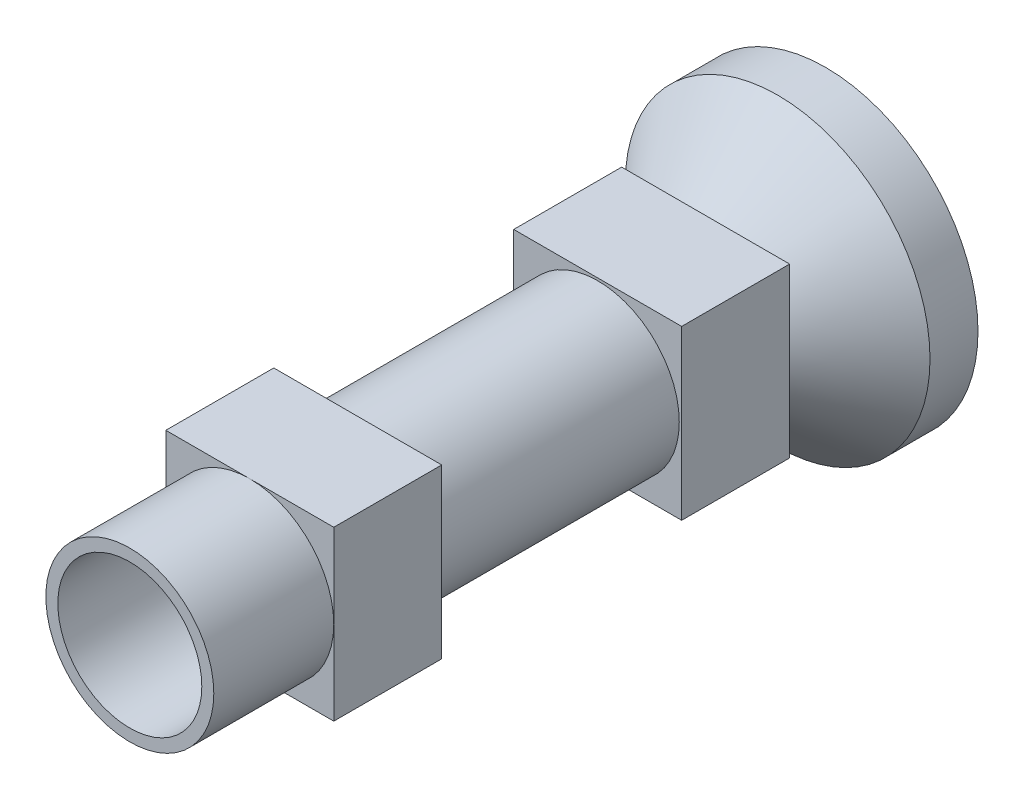
SolidWorks part; units mm, degrees
material "ABS"
ref_plane "正面" through (0, 0, 0) normal (0, 0, 1) x (1, 0, 0)
ref_plane "平面" through (0, 0, 0) normal (0, 1, 0) x (1, 0, 0)
ref_plane "右側面" through (0, 0, 0) normal (1, 0, 0) x (0, 0, -1)
sketch "ｽｹｯﾁ1" plane through (0, 0, 0) normal (0, 0, 1) x (1, 0, 0)
  circle A0 centre (0, 0) radius 3.5 construction
  circle A1 centre (0, 0) radius 6.35
  dimension "D1" = 7
  dimension "D2" = 12.7
ref_plane "平面1" through (0, 0, 5) normal (0, 0, 1) x (1, 0, 0)
sketch "ｽｹｯﾁ2" plane through (0, 0, 5) normal (0, 0, 1) x (1, 0, 0)
  circle A0 centre (0, 0) radius 3.5 construction
  circle A1 centre (0, 0) radius 3.5
ref_plane "平面2" through (0, 0, 29) normal (0, 0, 1) x (1, 0, 0)
ref_plane "平面3" through (0, 0, 24) normal (0, 0, 1) x (1, 0, 0)
sketch "ｽｹｯﾁ5" plane through (0, 0, 29) normal (0, 0, 1) x (1, 0, 0)
  circle A0 centre (0, 0) radius 6.35 construction
  circle A1 centre (0, 0) radius 6.35 construction
  circle A2 centre (0, 0) radius 3.5
  dimension "D1" = 7
extrude "ﾎﾞｽ - 押し出し3" add sketch "ｽｹｯﾁ2" along normal up to surface (19 mm away) contours A1 up to plane "平面3"
extrude "ﾎﾞｽ - 押し出し4" add sketch "ｽｹｯﾁ1" along normal blind 2 separate body
extrude "ﾎﾞｽ - 押し出し5" add sketch "ｽｹｯﾁ5" against normal blind 2 contours A1
loft "ﾛﾌﾄ1" add section face at (6.35, 0, 2) section face at (3.5, 0, 5)
loft "ﾛﾌﾄ2" add section face at (3.5, 0, 24) section face at (3.5, 0, 27)
ref_plane "平面5" through (0, 0, 14.5) normal (0, 0, 1) x (1, 0, 0)
ref_plane "平面6" through (0, 0, 15.25) normal (0, 0, 1) x (1, 0, 0)
sketch "ｽｹｯﾁ6" plane through (0, 0, 0) normal (0, 0, -1) x (-1, 0, 0)
  circle A0 centre (0, 0) radius 2.75
  dimension "D1" = 5.5
extrude "ｶｯﾄ - 押し出し1" cut sketch "ｽｹｯﾁ6" against normal blind 3
sketch "ｽｹｯﾁ7" plane through (0, 0, 3) normal (0, 0, -1) x (-1, 0, 0)
  circle A0 centre (0, 0) radius 1.8
  dimension "D1" = 3.6
extrude "ｶｯﾄ - 押し出し2" cut sketch "ｽｹｯﾁ7" against normal through all
sketch "ｽｹｯﾁ8" plane through (0, 0, 29) normal (0, 0, 1) x (1, 0, 0)
  circle A0 centre (0, 0) radius 3
  dimension "D1" = 6
extrude "ｶｯﾄ - 押し出し3" cut sketch "ｽｹｯﾁ8" against normal offset from surface (23 mm away) 3 up to face at (-1.8, 0, 3)
sketch "ｽｹｯﾁ12" plane through (0, 0, 0) normal (0, 0, -1) x (-1, 0, 0)
  line L0 (0, 0) -> (0, 2.75) construction
  line L1 (0, 0) -> (0.3745, 2.7244) construction
  line L2 (0, 0) -> (0.7419, 2.648) construction
  line L3 (0, 0) -> (1.0956, 2.5223) construction
  line L4 (0, 0) -> (1.4289, 2.3497) construction
  line L5 (0, 0) -> (1.7355, 2.1332) construction
  line L6 (0, 0) -> (2.0098, 1.877) construction
  line L7 (0, 0) -> (2.2467, 1.5859) construction
  line L8 (0, 0) -> (2.4417, 1.2652) construction
  line L9 (0, 0) -> (2.5912, 0.9209) construction
  line L10 (0, 0) -> (2.6925, 0.5595) construction
  line L11 (0, 0) -> (2.7436, 0.1877) construction
  line L12 (0, 0) -> (2.7436, -0.1877) construction
  line L13 (0, 0) -> (2.6925, -0.5595) construction
  line L14 (0, 0) -> (2.5912, -0.9209) construction
  line L15 (0, 0) -> (2.4417, -1.2652) construction
  line L16 (0, 0) -> (2.2467, -1.5859) construction
  line L17 (0, 0) -> (2.0098, -1.877) construction
  line L18 (0, 0) -> (1.7355, -2.1332) construction
  line L19 (0, 0) -> (1.4289, -2.3497) construction
  line L20 (0, 0) -> (1.0956, -2.5223) construction
  line L21 (0, 0) -> (0.7419, -2.648) construction
  line L22 (0, 0) -> (0.3745, -2.7244) construction
  line L23 (0, 0) -> (0, -2.75) construction
  line L24 (0, 0) -> (-0.3745, -2.7244) construction
  line L25 (0, 0) -> (-0.7419, -2.648) construction
  line L26 (0, 0) -> (-1.0956, -2.5223) construction
  line L27 (0, 0) -> (-1.4289, -2.3497) construction
  line L28 (0, 0) -> (-1.7355, -2.1332) construction
  line L29 (0, 0) -> (-2.0098, -1.877) construction
  line L30 (0, 0) -> (-2.2467, -1.5859) construction
  line L31 (0, 0) -> (-2.4417, -1.2652) construction
  line L32 (0, 0) -> (-2.5912, -0.9209) construction
  line L33 (0, 0) -> (-2.6925, -0.5595) construction
  line L34 (0, 0) -> (-2.7436, -0.1877) construction
  line L35 (0, 0) -> (-2.7436, 0.1877) construction
  line L36 (0, 0) -> (-2.6925, 0.5595) construction
  line L37 (0, 0) -> (-2.5912, 0.9209) construction
  line L38 (0, 0) -> (-2.4417, 1.2652) construction
  line L39 (0, 0) -> (-2.2467, 1.5859) construction
  line L40 (0, 0) -> (-2.0098, 1.877) construction
  line L41 (0, 0) -> (-1.7355, 2.1332) construction
  line L42 (0, 0) -> (-1.4289, 2.3497) construction
  line L43 (0, 0) -> (-1.0956, 2.5223) construction
  line L44 (0, 0) -> (-0.7419, 2.648) construction
  line L45 (0, 0) -> (-0.3745, 2.7244) construction
  line L46 (0, 0) -> (0.2081, 3.0429) construction
  line L47 (0.2081, 3.0429) -> (-0.0626, 2.7493)
  line L48 (-0.0626, 2.7493) -> (0, 0) construction
  line L49 (0, 0) -> (0.4364, 2.7152) construction
  line L50 (0.4364, 2.7152) -> (0.2081, 3.0429)
  line L51 (1.0214, 2.8739) -> (0.6815, 2.6642)
  line L52 (1.1527, 2.4967) -> (1.0214, 2.8739)
  line L53 (1.7589, 2.4918) -> (1.375, 2.3816)
  line L54 (1.7836, 2.0931) -> (1.7589, 2.4918)
  line L55 (2.3659, 1.9248) -> (1.9666, 1.9223)
  line L56 (2.2822, 1.5343) -> (2.3659, 1.9248)
  line L57 (2.7975, 1.2151) -> (2.4123, 1.3204)
  line L58 (2.6115, 0.8617) -> (2.7975, 1.2151)
  line L59 (3.0216, 0.4153) -> (2.679, 0.6206)
  line L60 (2.7472, 0.1252) -> (3.0216, 0.4153)
  line L61 (3.0216, -0.4153) -> (2.7472, -0.1252)
  line L62 (2.679, -0.6206) -> (3.0216, -0.4153)
  line L63 (2.7975, -1.2151) -> (2.6115, -0.8617)
  line L64 (2.4123, -1.3204) -> (2.7975, -1.2151)
  line L65 (2.3659, -1.9248) -> (2.2822, -1.5343)
  line L66 (1.9666, -1.9223) -> (2.3659, -1.9248)
  line L67 (1.7589, -2.4918) -> (1.7836, -2.0931)
  line L68 (1.375, -2.3816) -> (1.7589, -2.4918)
  line L69 (1.0214, -2.8739) -> (1.1527, -2.4967)
  line L70 (0.6815, -2.6642) -> (1.0214, -2.8739)
  line L71 (0.2081, -3.0429) -> (0.4364, -2.7152)
  line L72 (-0.0626, -2.7493) -> (0.2081, -3.0429)
  line L73 (-0.6205, -2.9862) -> (-0.3123, -2.7322)
  line L74 (-0.802, -2.6304) -> (-0.6205, -2.9862)
  line L75 (-1.4032, -2.708) -> (-1.0379, -2.5466)
  line L76 (-1.482, -2.3165) -> (-1.4032, -2.708)
  line L77 (-2.0818, -2.229) -> (-1.6865, -2.1722)
  line L78 (-2.052, -1.8308) -> (-2.0818, -2.229)
  line L79 (-2.606, -1.5847) -> (-2.21, -1.6366)
  line L80 (-2.4699, -1.2093) -> (-2.606, -1.5847)
  line L81 (-2.9369, -0.8229) -> (-2.5696, -0.9797)
  line L82 (-2.7045, -0.4981) -> (-2.9369, -0.8229)
  line L83 (-3.05, 0) -> (-2.7386, -0.2501)
  line L84 (-2.7386, 0.2501) -> (-3.05, 0)
  line L85 (-2.9369, 0.8229) -> (-2.7045, 0.4981)
  line L86 (-2.5696, 0.9797) -> (-2.9369, 0.8229)
  line L87 (-2.606, 1.5847) -> (-2.4699, 1.2093)
  line L88 (-2.21, 1.6366) -> (-2.606, 1.5847)
  line L89 (-2.0818, 2.229) -> (-2.052, 1.8308)
  line L90 (-1.6865, 2.1722) -> (-2.0818, 2.229)
  line L91 (-1.4032, 2.708) -> (-1.482, 2.3165)
  line L92 (-1.0379, 2.5466) -> (-1.4032, 2.708)
  line L93 (-0.6205, 2.9862) -> (-0.802, 2.6304)
  line L94 (-0.3123, 2.7322) -> (-0.6205, 2.9862)
  circle A0 centre (0, 0) radius 2.75 construction
  circle A1 centre (0, 0) radius 3.05 construction
  arc A2 (0, 2.75) -> (0.3745, 2.7244) centre (0, 0) cw construction
  circle A3 centre (0, 0) radius 2.75 construction
  arc A4 (-0.0626, 2.7493) -> (0.4364, 2.7152) centre (0, 0) cw
  arc A5 (0.6815, 2.6642) -> (1.1527, 2.4967) centre (0, 0) cw
  arc A6 (1.375, 2.3816) -> (1.7836, 2.0931) centre (0, 0) cw
  arc A7 (1.9666, 1.9223) -> (2.2822, 1.5343) centre (0, 0) cw
  arc A8 (2.4123, 1.3204) -> (2.6115, 0.8617) centre (0, 0) cw
  arc A9 (2.679, 0.6206) -> (2.7472, 0.1252) centre (0, 0) cw
  arc A10 (2.7472, -0.1252) -> (2.679, -0.6206) centre (0, 0) cw
  arc A11 (2.6115, -0.8617) -> (2.4123, -1.3204) centre (0, 0) cw
  arc A12 (2.2822, -1.5343) -> (1.9666, -1.9223) centre (0, 0) cw
  arc A13 (1.7836, -2.0931) -> (1.375, -2.3816) centre (0, 0) cw
  arc A14 (1.1527, -2.4967) -> (0.6815, -2.6642) centre (0, 0) cw
  arc A15 (0.4364, -2.7152) -> (-0.0626, -2.7493) centre (0, 0) cw
  arc A16 (-0.3123, -2.7322) -> (-0.802, -2.6304) centre (0, 0) cw
  arc A17 (-1.0379, -2.5466) -> (-1.482, -2.3165) centre (0, 0) cw
  arc A18 (-1.6865, -2.1722) -> (-2.052, -1.8308) centre (0, 0) cw
  arc A19 (-2.21, -1.6366) -> (-2.4699, -1.2093) centre (0, 0) cw
  arc A20 (-2.5696, -0.9797) -> (-2.7045, -0.4981) centre (0, 0) cw
  arc A21 (-2.7386, -0.2501) -> (-2.7386, 0.2501) centre (0, 0) cw
  arc A22 (-2.7045, 0.4981) -> (-2.5696, 0.9797) centre (0, 0) cw
  arc A23 (-2.4699, 1.2093) -> (-2.21, 1.6366) centre (0, 0) cw
  arc A24 (-2.052, 1.8308) -> (-1.6865, 2.1722) centre (0, 0) cw
  arc A25 (-1.482, 2.3165) -> (-1.0379, 2.5466) centre (0, 0) cw
  arc A26 (-0.802, 2.6304) -> (-0.3123, 2.7322) centre (0, 0) cw
  point P53 (0, 0)
  point P54 (0.1877, 2.7436)
  point P56 (0.1877, 2.7436)
  point P129 (0, 0)
  dimension "D2" = 6.1
  dimension "D3" = 10.435
  dimension "D1" = 46
  dimension "D4" = 23
extrude "ｶｯﾄ - 押し出し5" cut sketch "ｽｹｯﾁ12" against normal up to surface (3 mm away) up to face at (-1.8, 0, 3)
sketch "ｽｹｯﾁ14" plane through (0, 0, 24) normal (0, 0, 1) x (1, 0, 0)
  line L1 (3.5, -3.5) -> (-3.5, -3.5)
  line L2 (3.5, -3.5) -> (3.5, 3.5)
  line L3 (3.5, 3.5) -> (-3.5, 3.5)
  line L4 (-3.5, -3.5) -> (-3.5, 3.5)
  line L5 (3.5, -3.5) -> (-3.5, 3.5) construction
  line L6 (3.5, 3.5) -> (-3.5, -3.5) construction
  circle A0 centre (0, 0) radius 3.4
  circle A1 centre (0, 0) radius 3.5 construction
  point P0 (0, 0)
  dimension "D3" = 0.1
  dimension "D1" = 7
  dimension "D2" = 7
extrude "ﾎﾞｽ - 押し出し7" add sketch "ｽｹｯﾁ14" against normal blind 19
sketch "ｽｹｯﾁ16" plane through (0, 0, 14.5) normal (0, 0, 1) x (1, 0, 0)
  line L1 (3.5, -3.5) -> (-3.5, -3.5)
  line L2 (3.5, -3.5) -> (3.5, 3.5)
  line L3 (3.5, 3.5) -> (-3.5, 3.5)
  line L4 (-3.5, -3.5) -> (-3.5, 3.5)
  line L5 (3.5, -3.5) -> (-3.5, 3.5) construction
  line L6 (3.5, 3.5) -> (-3.5, -3.5) construction
  circle A0 centre (0, 0) radius 3.4
  arc A1 (0, 3.5) -> (-3.5, 0) centre (0, 0) ccw construction
  point P0 (0, 0)
  dimension "D1" = 0.1
extrude "ｶｯﾄ - 押し出し6" cut sketch "ｽｹｯﾁ16" against normal blind 5 and the other way blind 5
sketch "ｽｹｯﾁ17" plane through (0, 0, 6) normal (0, 0, 1) x (1, 0, 0)
  circle A0 centre (0, 0) radius 1.8 construction
  circle A1 centre (0, 0) radius 3
  circle A2 centre (0, 0) radius 3
  circle A3 centre (0, 0) radius 1.8
  dimension "D1" = 0
extrude "ﾎﾞｽ - 押し出し8" add sketch "ｽｹｯﾁ17" along normal offset from surface (14 mm away) 9 up to face at (3, 0, 29)
equation "\"D3@ｽｹｯﾁ12\"=360/23*2/3"
